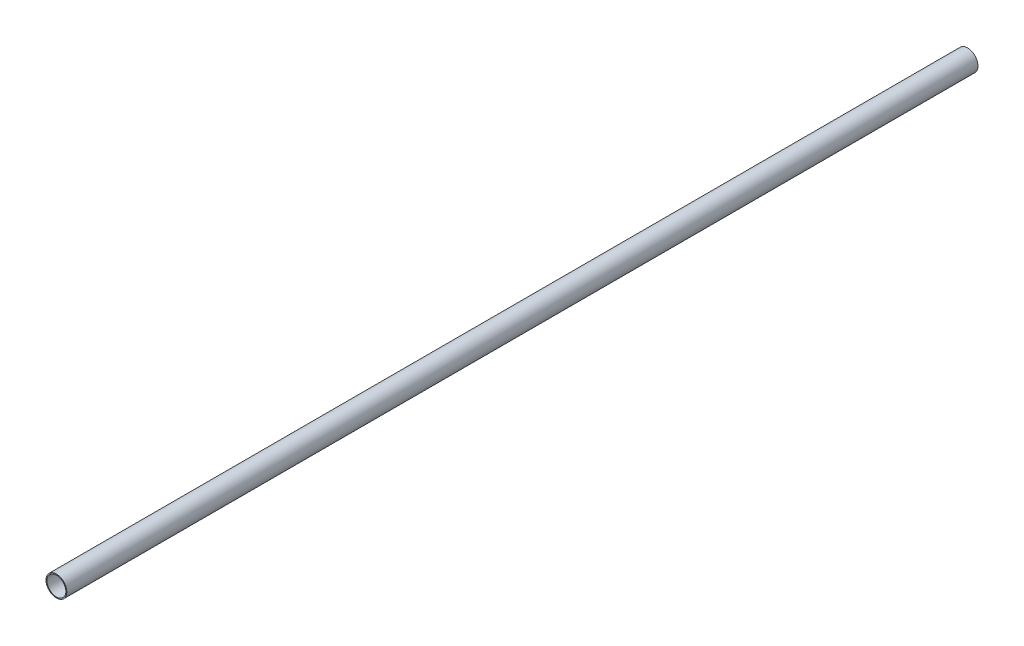
SolidWorks part; units mm, degrees
ref_plane "Plan de face" through (0, 0, 0) normal (0, 0, 1) x (1, 0, 0)
ref_plane "Plan de dessus" through (0, 0, 0) normal (0, 1, 0) x (1, 0, 0)
ref_plane "Plan de droite" through (0, 0, 0) normal (1, 0, 0) x (0, 0, -1)
sketch "Esquisse1" plane through (0, 0, 0) normal (0, 0, 1) x (1, 0, 0)
  circle A0 centre (0, 0) radius 14.5
  circle A1 centre (0, 0) radius 16
  dimension "D1" = 32
  dimension "D2" = 29
extrude "Boss.-Extru.1" add sketch "Esquisse1" along normal blind 1400
